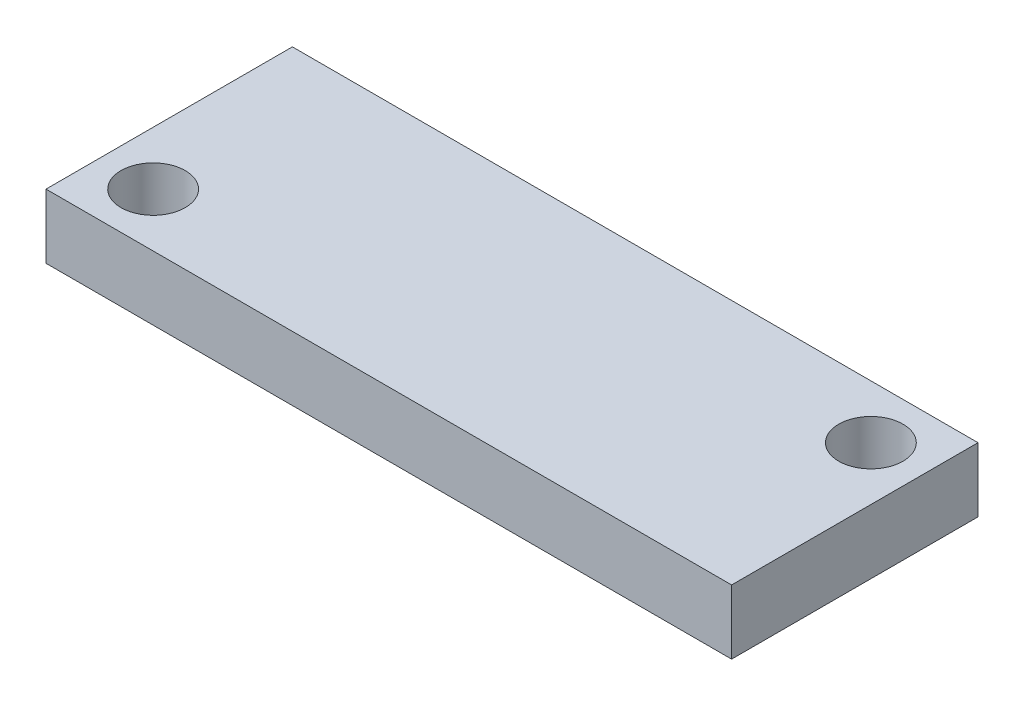
SolidWorks part; units mm, degrees
ref_plane "Front Plane" through (0, 0, 0) normal (0, 0, 1) x (1, 0, 0)
ref_plane "Top Plane" through (0, 0, 0) normal (0, 1, 0) x (1, 0, 0)
ref_plane "Right Plane" through (0, 0, 0) normal (1, 0, 0) x (0, 0, -1)
sketch "Sketch1" plane through (0, 0, 0) normal (0, 1, 0) x (1, 0, 0)
  line L0 (0, 2.5) -> (37.7113, 2.5) construction
  line L1 (0, 0) -> (32, 0)
  line L2 (0, 0) -> (0, 11.5)
  line L3 (32, 11.5) -> (32, 0)
  line L4 (0, 9) -> (32, 9) construction
  line L5 (0, 11.5) -> (32, 11.5)
  circle A0 centre (2.5, 2.5) radius 1.5
  circle A3 centre (29.5, 9) radius 1.5
  dimension "D3" = 3
  dimension "D4" = 32
  dimension "D5" = 9
  dimension "D6" = 3
  dimension "D7" = 2.5
  dimension "D1" = 2.5
  dimension "D2" = 2.5
  dimension "2.5" = 2.5
extrude "Boss-Extrude1" add sketch "Sketch1" along normal blind 3
